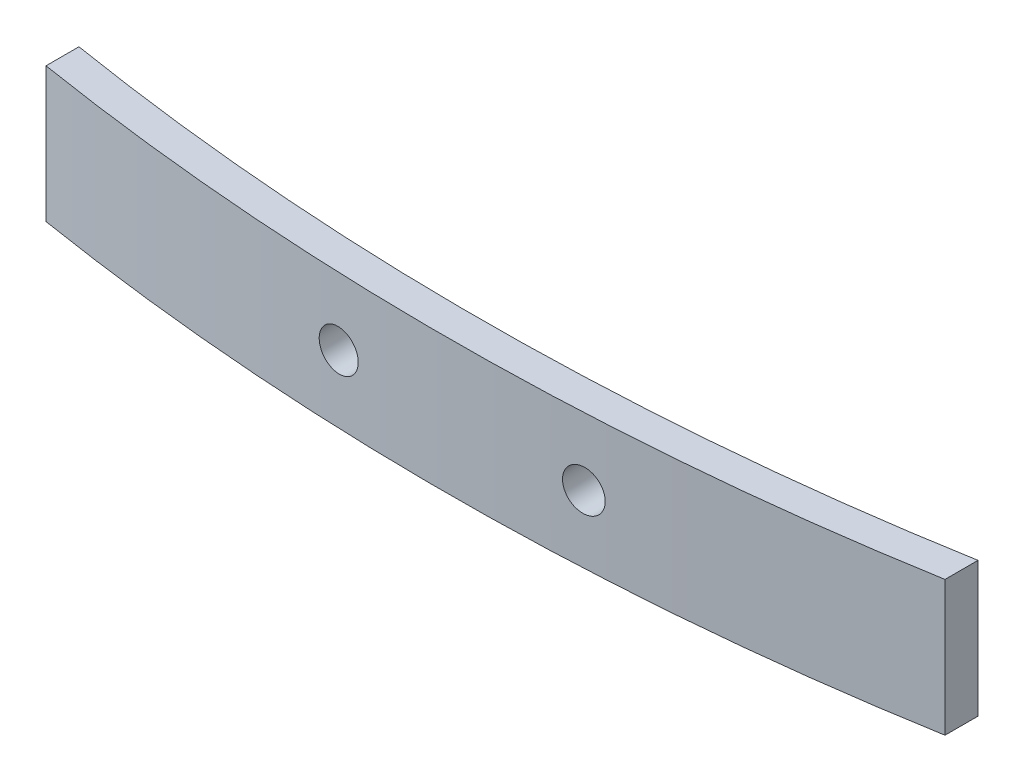
SolidWorks part; units mm, degrees
ref_plane "Front Plane" through (0, 0, 0) normal (0, 0, 1) x (1, 0, 0)
ref_plane "Top Plane" through (0, 0, 0) normal (0, 1, 0) x (1, 0, 0)
ref_plane "Right Plane" through (0, 0, 0) normal (1, 0, 0) x (0, 0, -1)
sketch "Sketch1" plane through (0, 0, 0) normal (0, 1, 0) x (1, 0, 0)
  line L0 (-35, 4.1426) -> (35, 4.5206) construction
  line L3 (-27.5, 11.9983) -> (-27.5, -12.2817) construction
  line L4 (27.5, 20.0549) -> (27.5, -12.2817) construction
  line L7 (27.5, 1.7531) -> (27.5, -0.2767)
  line L8 (-27.5, 1.4611) -> (-27.5, -0.5651)
  arc A4 (-27.5, 1.4611) -> (27.5, 1.7531) centre (-0.865, 164.5106) ccw
  arc A5 (-27.5, -0.5651) -> (27.5, -0.2767) centre (-0.865, 164.5106) ccw
  arc A7 (-35, 2.8648) -> (35, 3.2398) centre (-0.865, 164.5106) ccw construction
  arc A9 (-35.4132, 0.908) -> (35.4342, 1.2875) centre (-0.865, 164.5106) ccw construction
  point P4 (-35, 4.1426)
  point P7 (38.108, 5.4708)
  point P8 (35, 4.5206)
  point P18 (-31.892, 5.0928)
  dimension "D3" = 70
  dimension "D4" = 35
  dimension "D6" = 55
  dimension "D8" = 27.5
  dimension "D7" = 2
extrude "Boss-Extrude1" add sketch "Sketch1" along normal blind 8.3
sketch "Sketch2" plane through (0, 0, 0) normal (0, 0, 1) x (1, 0, 0)
  line L0 (0, 8.3) -> (0, 0) construction
  line L1 (27.5, 8.3) -> (-27.5, 8.3) construction
  circle A0 centre (7.5, 4.15) radius 1.25
  circle A1 centre (-7.5, 4.15) radius 1.25
  point P15 (0, 4.15)
  dimension "D2" = 2.5
  dimension "D3" = 2.5
  dimension "D1" = 15
  dimension "D4" = 7.5
extrude "Cut-Extrude1" cut sketch "Sketch2" against normal through all both and the other way through all
